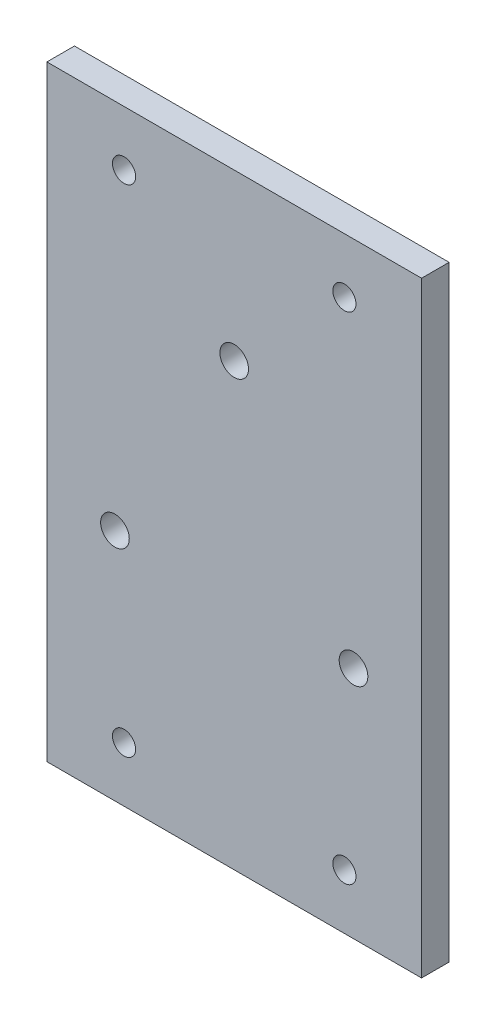
SolidWorks part; units mm, degrees
ref_plane "Front Plane" through (0, 0, 0) normal (0, 0, 1) x (1, 0, 0)
ref_plane "Top Plane" through (0, 0, 0) normal (0, 1, 0) x (1, 0, 0)
ref_plane "Right Plane" through (0, 0, 0) normal (1, 0, 0) x (0, 0, -1)
sketch "Sketch1" plane through (0, 0, 0) normal (0, 0, 1) x (1, 0, 0)
  line L1 (-34, 55) -> (34, 55)
  line L2 (-34, 55) -> (-34, -55)
  line L3 (-34, -55) -> (34, -55)
  line L4 (34, 55) -> (34, -55)
  line L5 (-34, 55) -> (34, -55) construction
  line L6 (-34, -55) -> (34, 55) construction
  line L7 (-20, 45) -> (20, 45) construction
  line L8 (-20, 45) -> (-20, -45) construction
  line L9 (-20, -45) -> (20, -45) construction
  line L10 (20, 45) -> (20, -45) construction
  line L11 (-20, 45) -> (20, -45) construction
  line L12 (-20, -45) -> (20, 45) construction
  line L13 (0, 25) -> (-21.6506, -12.5) construction
  line L14 (-21.6506, -12.5) -> (21.6506, -12.5) construction
  line L15 (21.6506, -12.5) -> (0, 25) construction
  circle A0 centre (20, 45) radius 2.1
  circle A1 centre (-20, 45) radius 2.1
  circle A2 centre (20, -45) radius 2.1
  circle A3 centre (-20, -45) radius 2.1
  circle A4 centre (0, 0) radius 25 construction
  circle A5 centre (21.6506, -12.5) radius 2.6
  circle A6 centre (0, 25) radius 2.6
  circle A7 centre (-21.6506, -12.5) radius 2.6
  point P0 (0, 0)
  point P6 (0, 0)
extrude "Boss-Extrude1" add sketch "Sketch1" along normal blind 5
